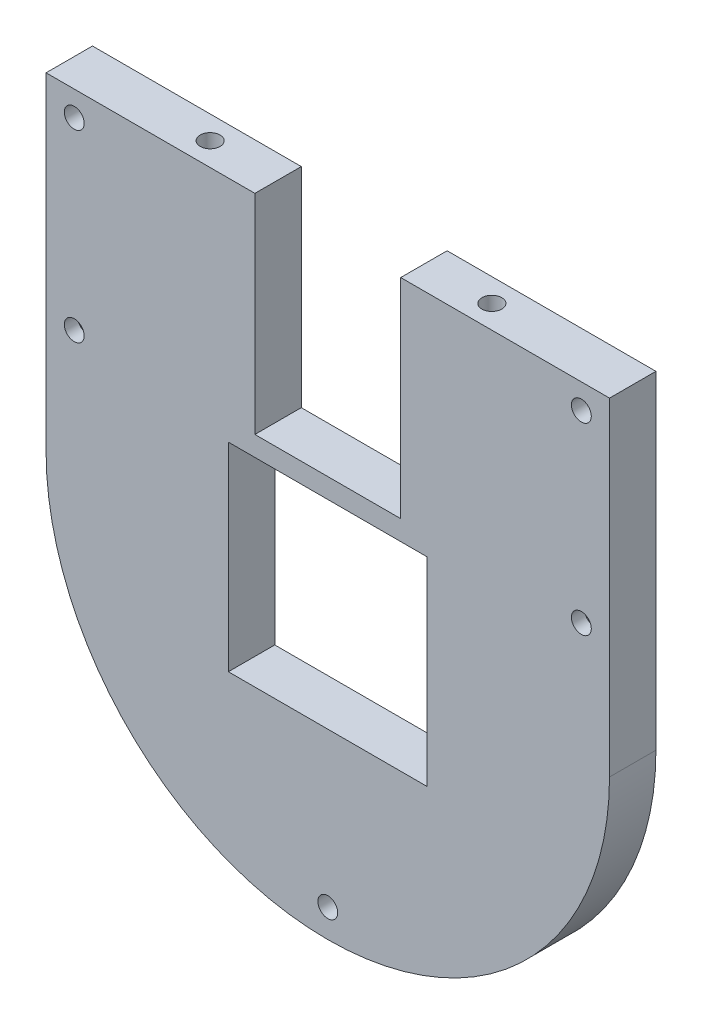
SolidWorks part; units mm, degrees
ref_plane "Front Plane" through (0, 0, 0) normal (0, 0, 1) x (1, 0, 0)
ref_plane "Top Plane" through (0, 0, 0) normal (0, 1, 0) x (1, 0, 0)
ref_plane "Right Plane" through (0, 0, 0) normal (1, 0, 0) x (0, 0, -1)
sketch "Sketch1" plane through (0, 0, 0) normal (0, 0, 1) x (1, 0, 0)
  line L1 (0, 0) -> (85, 0)
  line L2 (0, 0) -> (0, 95)
  line L3 (0, 95) -> (85, 95)
  line L4 (85, 0) -> (85, 95)
  dimension "D1" = 95
  dimension "D2" = 85
extrude "Boss-Extrude1" add sketch "Sketch1" along normal blind 7
sketch "Sketch2" plane through (0, 0, 7) normal (0, 0, 1) x (1, 0, 0)
  line L0 (0, 0) -> (85, 0) construction
  line L1 (27.5, 30) -> (57.5, 30)
  line L2 (27.5, 30) -> (27.5, 60)
  line L3 (27.5, 60) -> (57.5, 60)
  line L4 (57.5, 30) -> (57.5, 60)
  line L5 (27.5, 30) -> (57.5, 60) construction
  line L6 (27.5, 60) -> (57.5, 30) construction
  point P0 (42.5, 45)
  point P7 (42.5, 0)
  dimension "D1" = 0
  dimension "D2" = 30
  dimension "D3" = 30
  dimension "D4" = 45
extrude "Cut-Extrude1" cut sketch "Sketch2" against normal blind 7
sketch "Sketch4" plane through (0, 95, 0) normal (0, 1, 0) x (1, 0, 0)
  line L0 (0, -3.5) -> (85, -3.5) construction
  line L1 (0, -7) -> (0, 0) construction
  line L2 (85, -7) -> (85, 0) construction
  circle A0 centre (21.25, -3.5) radius 1.5
  circle A1 centre (63.75, -3.5) radius 1.5
  dimension "D1" = 3
  dimension "D2" = 3
  dimension "D3" = 21.25
  dimension "D4" = 21.25
extrude "Cut-Extrude2" cut sketch "Sketch4" against normal blind 10.5
sketch "Sketch6" plane through (0, 0, 0) normal (0, 0, -1) x (-1, 0, 0)
  line L0 (-85, 95) -> (0, 95) construction
  line L1 (-85, 0) -> (-85, 95) construction
  line L2 (-42.5, 60) -> (-42.5, 65.8033) construction
  line L3 (-57.5, 60) -> (-27.5, 60) construction
  line L4 (0, 95) -> (0, 0) construction
  line L5 (0, 0) -> (-85, 0) construction
  circle A0 centre (-80.75, 90.75) radius 1.5
  circle A1 centre (-4.25, 90.75) radius 1.5
  circle A2 centre (-4.45, 4.25) radius 1.5
  circle A3 centre (-80.75, 7.25) radius 1.5
  dimension "D1" = 3
  dimension "D5" = 3
  dimension "D7" = 3
  dimension "D2" = 4.25
  dimension "D3" = 4.25
  dimension "D4" = 4.45
  dimension "D6" = 4.25
  dimension "D8" = 7.25
  dimension "D9" = 4.25
extrude "Cut-Extrude3" cut sketch "Sketch6" against normal blind 8
sketch "Sketch7" plane through (0, 0, 0) normal (0, 0, -1) x (-1, 0, 0)
  line L0 (-85, 45) -> (-85, 0)
  line L1 (-85, 0) -> (0, 0)
  line L2 (0, 0) -> (0, 45)
  arc A0 (-85, 45) -> (0, 45) centre (-42.5, 45) ccw
  dimension "D1" = 85
extrude "Cut-Extrude4" cut sketch "Sketch7" against normal blind 10
sketch "Sketch8" plane through (0, 0, 7) normal (0, 0, 1) x (1, 0, 0)
  line L0 (85, 95) -> (0, 95) construction
  line L1 (85, 45) -> (85, 95) construction
  line L2 (42.5, 60) -> (42.5, 67.7032) construction
  line L3 (57.5, 60) -> (27.5, 60) construction
  circle A0 centre (80.75, 63) radius 1.5
  circle A1 centre (4.25, 63) radius 1.5
  dimension "D1" = 3
  dimension "D2" = 32
  dimension "D3" = 4.25
extrude "Cut-Extrude5" cut sketch "Sketch8" against normal blind 10
sketch "Sketch9" plane through (0, 0, 0) normal (0, 0, -1) x (-1, 0, 0)
  line L0 (-27.5, 30) -> (-57.5, 30) construction
  line L1 (-79.045, 65.9531) -> (-82.455, 65.9531)
  line L2 (-82.455, 65.9531) -> (-84.16, 63)
  line L3 (-84.16, 63) -> (-82.455, 60.0469)
  line L4 (-82.455, 60.0469) -> (-79.045, 60.0469)
  line L5 (-79.045, 60.0469) -> (-77.34, 63)
  line L6 (-77.34, 63) -> (-79.045, 65.9531)
  line L7 (-42.5, 60) -> (-42.5, 65.7072) construction
  line L8 (-57.5, 60) -> (-27.5, 60) construction
  line L9 (-0.84, 63) -> (-2.545, 60.0469)
  line L10 (-2.545, 65.9531) -> (-0.84, 63)
  line L11 (-5.955, 65.9531) -> (-2.545, 65.9531)
  line L12 (-7.66, 63) -> (-5.955, 65.9531)
  line L13 (-5.955, 60.0469) -> (-7.66, 63)
  line L14 (-2.545, 60.0469) -> (-5.955, 60.0469)
  circle A0 centre (-80.75, 63) radius 2.9531 construction
  dimension "D1" = 3.41
extrude "Cut-Extrude6" cut sketch "Sketch9" against normal blind 5
sketch "Sketch10" plane through (0, 0, 0) normal (0, 0, -1) x (-1, 0, 0)
  line L0 (-42.5, 2.5) -> (-42.5, 26.8409) construction
  arc A0 (-85, 45) -> (0, 45) centre (-42.5, 45) ccw construction
  circle A1 centre (-42.5, 6.75) radius 1.5
  dimension "D1" = 3
  dimension "D2" = 4.25
sketch "Sketch11" plane through (0, 0, 7) normal (0, 0, 1) x (1, 0, 0)
  circle A0 centre (42.5, 6.75) radius 1.5 construction
  circle A1 centre (42.5, 6.75) radius 1.5
extrude "Cut-Extrude8" cut sketch "Sketch11" against normal blind 4
sketch "Sketch12" plane through (0, 0, 0) normal (0, 0, -1) x (-1, 0, 0)
  line L0 (-85, 95) -> (0, 95) construction
  line L1 (-53.5, 95) -> (-31.5, 95)
  line L2 (-57.5, 60) -> (-27.5, 60) construction
  line L3 (-53.5, 95) -> (-31.5, 95)
  line L4 (-53.5, 95) -> (-53.5, 63)
  line L5 (-53.5, 63) -> (-31.5, 63)
  line L6 (-31.5, 95) -> (-31.5, 63)
  point P0 (-42.5, 95)
  point P6 (-42.5, 95)
  line M17 (0, 95) -> (-85, 95)
  dimension "D1" = 22
  dimension "D2" = 0
  dimension "D3" = 3
extrude "Cut-Extrude9" cut sketch "Sketch12" against normal blind 10 contours L6 L4 L5 M17
sketch "Sketch13" plane through (0, 95, 0) normal (0, 1, 0) x (1, 0, 0)
  line L1 (0, 0) -> (31.5, 0)
  line L2 (0, 0) -> (0, -7)
  line L3 (0, -7) -> (31.5, -7)
  line L4 (31.5, 0) -> (31.5, -7)
  line L5 (53.5, 0) -> (85, 0)
  line L6 (53.5, 0) -> (53.5, -7)
  line L7 (53.5, -7) -> (85, -7)
  line L8 (85, 0) -> (85, -7)
  circle A0 centre (21.25, -3.5) radius 1.5
  circle A1 centre (63.75, -3.5) radius 1.5
extrude "Cut-Extrude10" cut sketch "Sketch13" against normal blind 0.5
